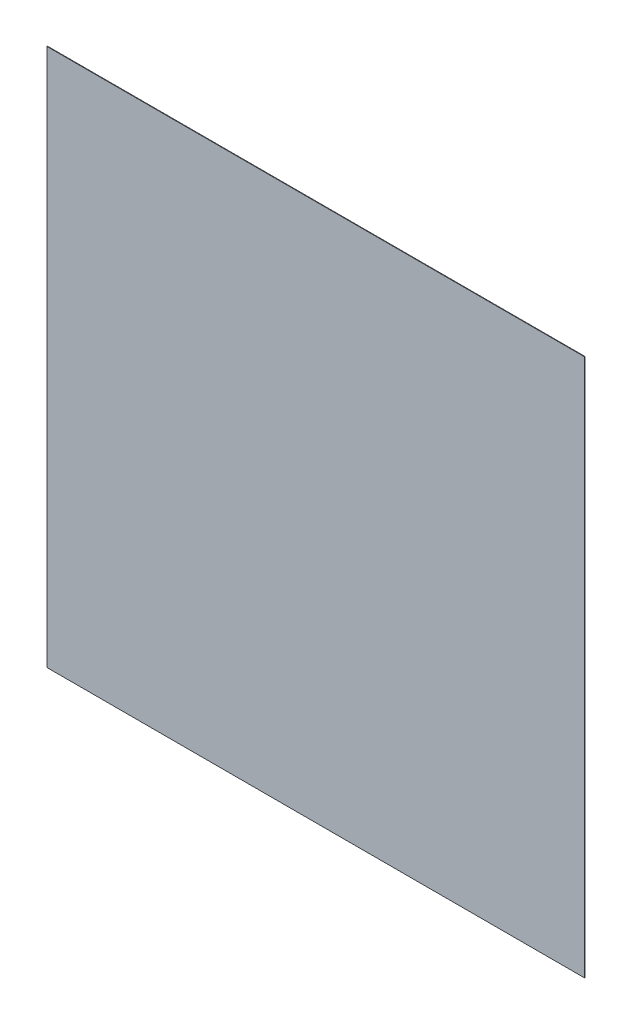
SolidWorks part; units mm, degrees
ref_plane "Front Plane" through (0, 0, 0) normal (0, 0, 1) x (1, 0, 0)
ref_plane "Top Plane" through (0, 0, 0) normal (0, 1, 0) x (1, 0, 0)
ref_plane "Right Plane" through (0, 0, 0) normal (1, 0, 0) x (0, 0, -1)
sketch "Sketch1" plane through (0, 0, 0) normal (0, 0, 1) x (1, 0, 0)
  line L1 (-307.5269, 151.3924) -> (692.4731, 151.3924)
  line L2 (-307.5269, 151.3924) -> (-307.5269, -848.6076)
  line L3 (-307.5269, -848.6076) -> (692.4731, -848.6076)
  line L4 (692.4731, 151.3924) -> (692.4731, -848.6076)
  point P4 (-449.5653, 154.6452)
  point P6 (-307.5269, 151.3924)
  dimension "D1" = 1000
  dimension "D2" = 1000
extrude "Boss-Extrude1" add sketch "Sketch1" along normal blind 1
